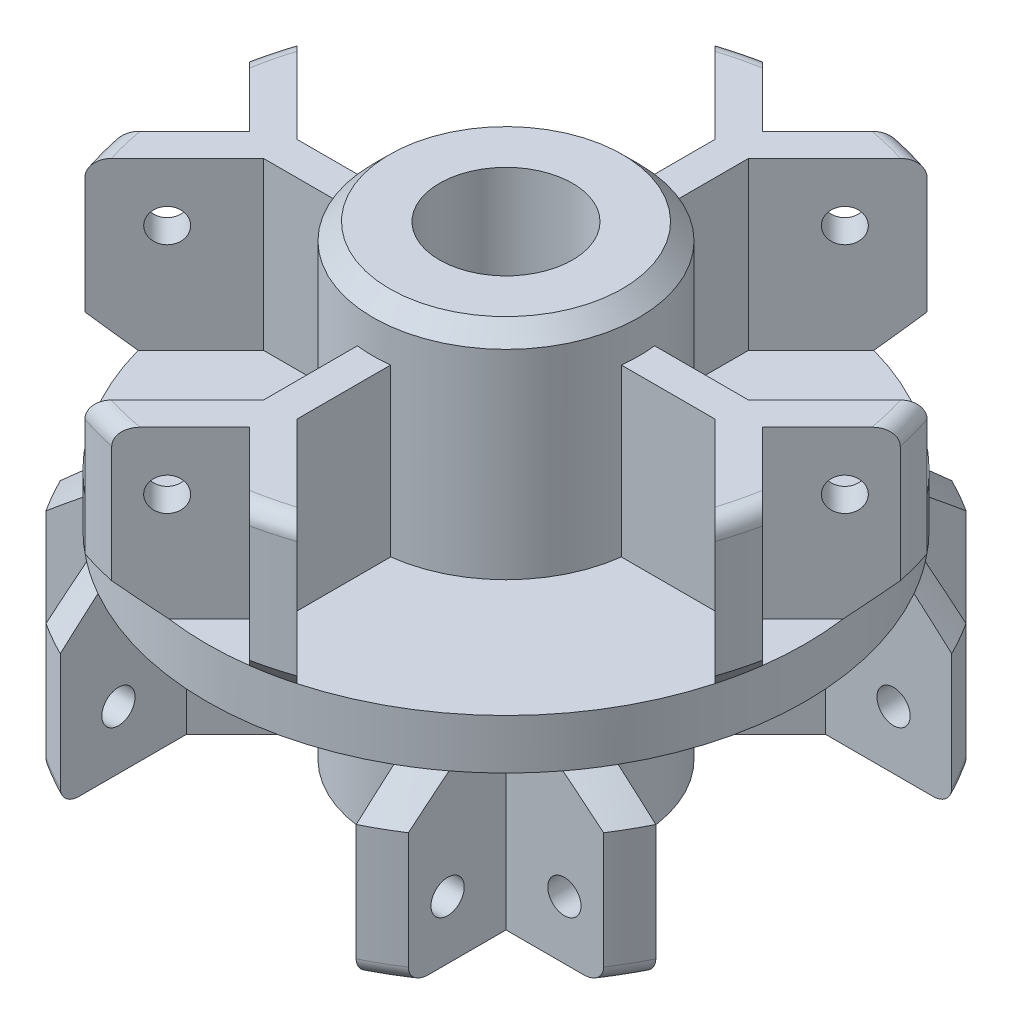
SolidWorks part; units mm, degrees
material "ABS generico"
ref_plane "Piano frontale" through (0, 0, 0) normal (0, 0, 1) x (1, 0, 0)
ref_plane "Piano superiore" through (0, 0, 0) normal (0, 1, 0) x (1, 0, 0)
ref_plane "Piano destro" through (0, 0, 0) normal (1, 0, 0) x (0, 0, -1)
sketch "Schizzo2" plane through (0, 0, 0) normal (0, 1, 0) x (1, 0, 0)
  circle A0 centre (0, 0) radius 20
  dimension "D1" = 40
extrude "Estrusione-Estrusione1" add sketch "Schizzo2" along normal mid plane 29
sketch "Schizzo3" plane through (0, 14.5, 0) normal (0, 1, 0) x (1, 0, 0)
  circle A0 centre (0, 0) radius 8
  dimension "D1" = 16
extrude "Taglio-Estrusione1" cut sketch "Schizzo3" against normal blind 13 flip side to cut
mirror "Specchia2" about plane through (0, 0, 0) normal (0, 1, 0) of "Taglio-Estrusione1"
sketch "Schizzo6" plane through (0, 1.5, 0) normal (0, 1, 0) x (1, 0, 0)
  line L0 (0, 8) -> (0, 14) construction
  line L1 (0, 14) -> (-5.2882, 19.2882) construction
  line L2 (0, 14) -> (5.2882, 19.2882) construction
  line L3 (1, 7.9373) -> (1, 13.5858)
  line L4 (0, 15.4142) -> (-4.1504, 19.5646)
  line L5 (1, 13.5858) -> (6.372, 18.9578)
  line L6 (-1, 7.9373) -> (-1, 13.5858)
  line L7 (-1, 13.5858) -> (-6.372, 18.9578)
  line L8 (0, 15.4142) -> (4.1504, 19.5646)
  line L9 (-0.7071, 13.2929) -> (-5.9953, 18.5811) construction
  line L10 (0.7071, 13.2929) -> (5.9953, 18.5811) construction
  line L11 (1, 8) -> (1, 14) construction
  line L12 (-1, 8) -> (-1, 14) construction
  line L13 (-0.7071, 14.7071) -> (4.5811, 19.9953) construction
  line L14 (0.7071, 14.7071) -> (-4.5811, 19.9953) construction
  line L15 (13.5858, 1) -> (18.9578, 6.372)
  line L16 (15.4142, 0) -> (19.5646, 4.1504)
  line L17 (15.4142, 0) -> (19.5646, -4.1504)
  line L18 (13.5858, -1) -> (18.9578, -6.372)
  line L19 (7.9373, -1) -> (13.5858, -1)
  line L20 (7.9373, 1) -> (13.5858, 1)
  line L21 (1, -13.5858) -> (6.372, -18.9578)
  line L22 (0, -15.4142) -> (4.1504, -19.5646)
  line L23 (0, -15.4142) -> (-4.1504, -19.5646)
  line L24 (-1, -13.5858) -> (-6.372, -18.9578)
  line L25 (-1, -7.9373) -> (-1, -13.5858)
  line L26 (1, -7.9373) -> (1, -13.5858)
  line L27 (-13.5858, -1) -> (-18.9578, -6.372)
  line L28 (-15.4142, 0) -> (-19.5646, -4.1504)
  line L29 (-15.4142, 0) -> (-19.5646, 4.1504)
  line L30 (-13.5858, 1) -> (-18.9578, 6.372)
  line L31 (-7.9373, 1) -> (-13.5858, 1)
  line L32 (-7.9373, -1) -> (-13.5858, -1)
  circle A0 centre (0, 0) radius 8 construction
  circle A1 centre (0, 0) radius 8 construction
  circle A2 centre (0, 0) radius 20 construction
  arc A3 (-6.372, 18.9578) -> (-4.1504, 19.5646) centre (0, 0) cw
  arc A4 (4.1504, 19.5646) -> (6.372, 18.9578) centre (0, 0) cw
  arc A5 (-1, 7.9373) -> (1, 7.9373) centre (0, 0) cw
  arc A6 (7.9373, 1) -> (7.9373, -1) centre (0, 0) cw
  arc A7 (18.9578, 6.372) -> (19.5646, 4.1504) centre (0, 0) cw
  arc A8 (19.5646, -4.1504) -> (18.9578, -6.372) centre (0, 0) cw
  arc A9 (1, -7.9373) -> (-1, -7.9373) centre (0, 0) cw
  arc A10 (6.372, -18.9578) -> (4.1504, -19.5646) centre (0, 0) cw
  arc A11 (-4.1504, -19.5646) -> (-6.372, -18.9578) centre (0, 0) cw
  arc A12 (-7.9373, -1) -> (-7.9373, 1) centre (0, 0) cw
  arc A13 (-18.9578, -6.372) -> (-19.5646, -4.1504) centre (0, 0) cw
  arc A14 (-19.5646, 4.1504) -> (-18.9578, 6.372) centre (0, 0) cw
  point P66 (0, 0)
  dimension "D5" = 4
  dimension "D1" = 6
  dimension "D2" = 135
  dimension "D3" = 1
  dimension "D4" = 1
extrude "Estrusione-Estrusione2" add sketch "Schizzo6" along normal blind 10
sketch "Schizzo20" plane through (0, -1.5, 0) normal (0, -1, 0) x (-1, 0, 0)
  line L0 (5.6569, -5.6569) -> (9.8995, -9.8995) construction
  line L1 (9.8995, -9.8995) -> (17.3781, -9.8995) construction
  line L2 (9.8995, -9.8995) -> (9.8995, -17.3781) construction
  line L3 (4.9054, -6.3196) -> (8.8995, -10.3137)
  line L4 (10.8995, -10.8995) -> (16.769, -10.8995)
  line L5 (8.8995, -10.3137) -> (8.8995, -17.9109)
  line L6 (6.3196, -4.9054) -> (10.3137, -8.8995)
  line L7 (10.3137, -8.8995) -> (17.9109, -8.8995)
  line L8 (10.8995, -10.8995) -> (10.8995, -16.769)
  line L9 (-4.9054, -6.3196) -> (-8.8995, -10.3137)
  line L10 (9.8995, -10.8995) -> (17.3781, -10.8995) construction
  line L11 (10.8995, -9.8995) -> (10.8995, -17.3781) construction
  line L12 (6.364, -4.9497) -> (10.6066, -9.1924) construction
  line L13 (4.9497, -6.364) -> (9.1924, -10.6066) construction
  line L14 (8.8995, -9.8995) -> (8.8995, -17.3781) construction
  line L15 (9.8995, -8.8995) -> (17.3781, -8.8995) construction
  line L16 (-6.3196, -4.9054) -> (-10.3137, -8.8995)
  line L17 (-10.3137, -8.8995) -> (-17.9109, -8.8995)
  line L18 (-10.8995, -10.8995) -> (-16.769, -10.8995)
  line L19 (-10.8995, -10.8995) -> (-10.8995, -16.769)
  line L20 (-8.8995, -10.3137) -> (-8.8995, -17.9109)
  line L21 (-6.3196, 4.9054) -> (-10.3137, 8.8995)
  line L22 (-4.9054, 6.3196) -> (-8.8995, 10.3137)
  line L23 (-8.8995, 10.3137) -> (-8.8995, 17.9109)
  line L24 (-10.8995, 10.8995) -> (-10.8995, 16.769)
  line L25 (-10.8995, 10.8995) -> (-16.769, 10.8995)
  line L26 (-10.3137, 8.8995) -> (-17.9109, 8.8995)
  line L27 (4.9054, 6.3196) -> (8.8995, 10.3137)
  line L28 (6.3196, 4.9054) -> (10.3137, 8.8995)
  line L29 (10.3137, 8.8995) -> (17.9109, 8.8995)
  line L30 (10.8995, 10.8995) -> (16.769, 10.8995)
  line L31 (10.8995, 10.8995) -> (10.8995, 16.769)
  line L32 (8.8995, 10.3137) -> (8.8995, 17.9109)
  circle A0 centre (0, 0) radius 8 construction
  circle A1 centre (0, 0) radius 20 construction
  circle A2 centre (0, 0) radius 8 construction
  arc A3 (6.3196, -4.9054) -> (4.9054, -6.3196) centre (0, 0) cw
  arc A4 (17.9109, -8.8995) -> (16.769, -10.8995) centre (0, 0) cw
  arc A5 (10.8995, -16.769) -> (8.8995, -17.9109) centre (0, 0) cw
  arc A6 (-4.9054, -6.3196) -> (-6.3196, -4.9054) centre (0, 0) cw
  arc A7 (-16.769, -10.8995) -> (-17.9109, -8.8995) centre (0, 0) cw
  arc A8 (-8.8995, -17.9109) -> (-10.8995, -16.769) centre (0, 0) cw
  arc A9 (-6.3196, 4.9054) -> (-4.9054, 6.3196) centre (0, 0) cw
  arc A10 (-10.8995, 16.769) -> (-8.8995, 17.9109) centre (0, 0) cw
  arc A11 (-17.9109, 8.8995) -> (-16.769, 10.8995) centre (0, 0) cw
  arc A12 (4.9054, 6.3196) -> (6.3196, 4.9054) centre (0, 0) cw
  arc A13 (16.769, 10.8995) -> (17.9109, 8.8995) centre (0, 0) cw
  arc A14 (8.8995, 17.9109) -> (10.8995, 16.769) centre (0, 0) cw
  point P66 (0, 0)
  dimension "D6" = 4
  dimension "D1" = 6
  dimension "D2" = 135
  dimension "D3" = 135
  dimension "D4" = 1
  dimension "D5" = 1
extrude "Estrusione-Estrusione3" add sketch "Schizzo20" along normal blind 10
chamfer "Smusso1" distance 1 angle 45 2 edges at (0, 14.5, 8) (0, -14.5, 8)
fillet "Raccordo1" radius 1 16 edges at (-19.2932, 11.5, 5.2699) (-19.2932, 11.5, -5.2699) (-5.2699, 11.5, -19.2932) (5.2699, 11.5, -19.2932) (19.2932, 11.5, -5.2699) (19.2932, 11.5, 5.2699) (-5.2699, 11.5, 19.2932) (5.2699, 11.5, 19.2932) (-17.3688, -11.5, -9.9159) (-9.9159, -11.5, -17.3688) (9.9159, -11.5, -17.3688) (17.3688, -11.5, -9.9159) (17.3688, -11.5, 9.9159) (9.9159, -11.5, 17.3688) (-9.9159, -11.5, 17.3688) (-17.3688, -11.5, 9.9159)
sketch "Schizzo11" plane through (0, 14.5, 0) normal (0, 1, 0) x (1, 0, 0)
  circle A0 centre (0, 0) radius 4
  dimension "D1" = 8
extrude "Taglio-Estrusione2" cut sketch "Schizzo11" against normal through all
ref_axis "Assi1" through (0, -14.5, 0) along (0, 1, 0)
sketch "Schizzo22" plane through (0, 0, 0) normal (1, 0, 0) x (0, 0, -1)
  line L1 (-18, 1.5) -> (-20, 3.5)
  line L2 (-18.9578, 1.5) -> (-13.5858, 1.5) construction
  line L3 (-18, 1.5) -> (-18, -1.5)
  line L4 (-20, -1.5) -> (-17.9109, -1.5) construction
  line L6 (-20, -1.5) -> (-20, 1.5)
  line L7 (-20, 3.5) -> (-20, 1.5)
  line L8 (-18, -1.5) -> (-20, -3.5)
  line L9 (-20, -3.5) -> (-20, -1.5)
  dimension "D1" = 2
revolve "Taglia-Rivoluzione1" cut sketch "Schizzo22" angle 360 about axis through (0, -14.5, 0) along (0, 1, 0)
hole_wizard "Foro Ø2.0 (2)-1" positions "Schizzo24" profile "Schizzo23" hole size "Ø2.0" standard "Ansi Metric" end condition through all
sketch "Schizzo24" plane through (7.7071, 0, 7.7071) normal (0.7071, 0, 0.7071) x (0.7071, 0, -0.7071)
  line L0 (-15.5628, 11.5) -> (-10.8995, 11.5) construction
  line L1 (-17.9109, 10.5) -> (-17.9109, 3.5) construction
  point P0 (-14.4109, 8)
  dimension "D1" = 3.5
  dimension "D2" = 3.5
sketch "Schizzo23" plane through (-2.4829, 8, 17.8971) normal (0, 1, 0) x (0.7071, 0, -0.7071)
  line L0 (0, 0) -> (0, 38.6982)
  line L1 (0, 38.6982) -> (1, 38.6982)
  line L2 (1, 38.6982) -> (1, 0)
  line L5 (1, 0) -> (0, 0)
  line L11 (0, -6.35) -> (0, 107.95) construction
  dimension "Thru Hole Dia." = 2
  dimension "Thru Hole Depth" = 38.6982
pattern_circular "RipetizioneCircolare1" count 4 over 360 about axis through (0, -14.5, 0) along (0, 1, 0) of "Foro Ø2.0 (2)-1"
hole_wizard "Foro Ø2.0 (2)-2" positions "Schizzo26" profile "Schizzo25" hole size "Ø2.0" standard "Ansi Metric"
sketch "Schizzo26" plane through (10.8995, 0, 0) normal (1, 0, 0) x (0, 0, -1)
  line L0 (-10.8995, -11.5) -> (-15.5628, -11.5) construction
  line L1 (-17.9109, -10.5) -> (-17.9109, -3.5) construction
  point P0 (-14.4109, -8)
  dimension "D1" = 3.5
  dimension "D2" = 3.5
sketch "Schizzo25" plane through (10.8995, -8, 14.4109) normal (0, 1, 0) x (0, 0, -1)
  line L0 (0, 0) -> (0, 39.3009)
  line L1 (0, 39.3009) -> (1, 38.7)
  line L2 (1, 38.7) -> (1, 0)
  line L5 (1, 0) -> (0, 0)
  line L10 (0, 39.3009) -> (-1, 38.7) construction
  line L11 (0, -6.35) -> (0, 107.95) construction
  dimension "Hole Dia." = 2
  dimension "Hole Depth" = 38.7
  dimension "Drill Angle" = 118
pattern_circular "RipetizioneCircolare2" count 4 over 360 about axis through (0, -14.5, 0) along (0, 1, 0) of "Foro Ø2.0 (2)-2"
